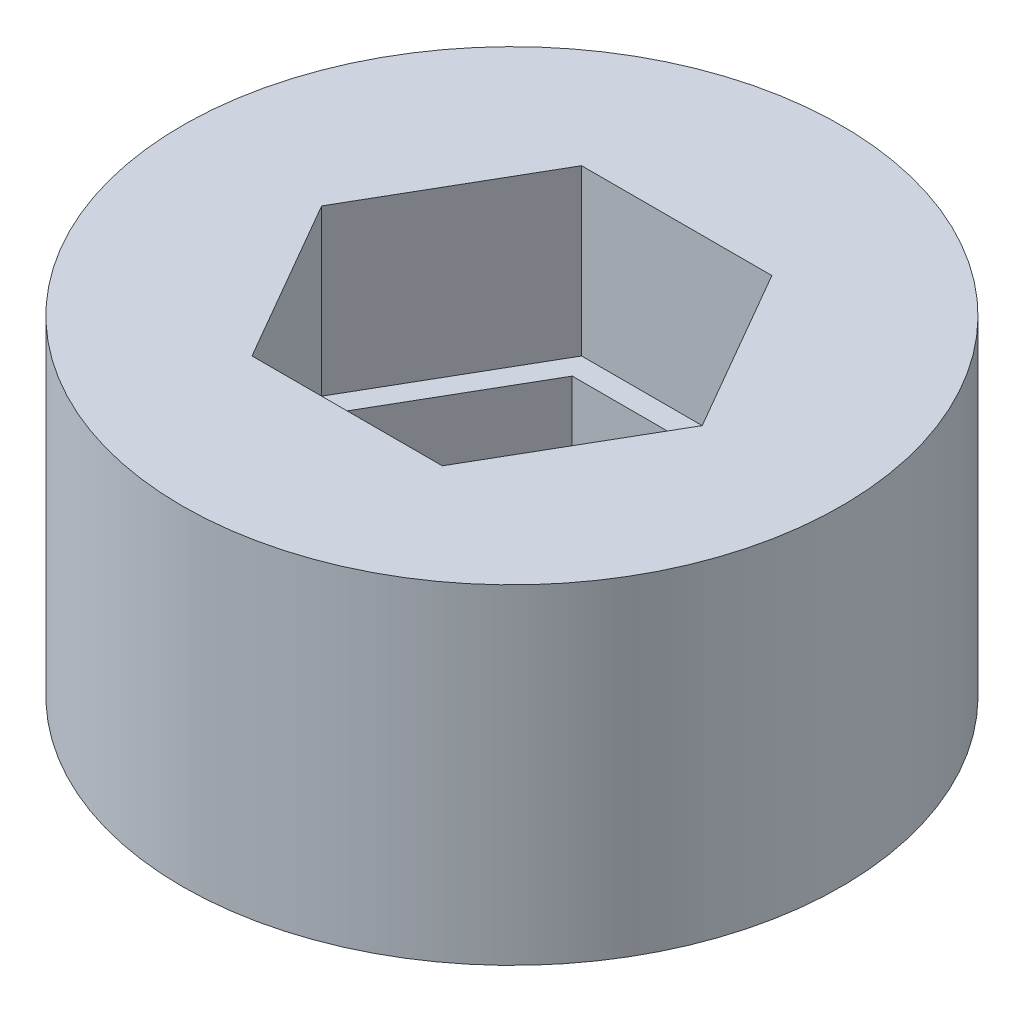
SolidWorks part; units mm, degrees
ref_plane "Front" through (0, 0, 0) normal (0, 0, 1) x (1, 0, 0)
ref_plane "Top" through (0, 0, 0) normal (0, 1, 0) x (1, 0, 0)
ref_plane "Right" through (0, 0, 0) normal (1, 0, 0) x (0, 0, -1)
sketch "Sketch1" plane through (0, 0, 0) normal (0, 1, 0) x (1, 0, 0)
  line L1 (1.5875, 2.7496) -> (-1.5875, 2.7496)
  line L2 (-1.5875, 2.7496) -> (-3.175, 0)
  line L3 (-3.175, 0) -> (-1.5875, -2.7496)
  line L4 (-1.5875, -2.7496) -> (1.5875, -2.7496)
  line L5 (1.5875, -2.7496) -> (3.175, 0)
  line L6 (3.175, 0) -> (1.5875, 2.7496)
  circle A0 centre (0, 0) radius 6.35
  circle A1 centre (0, 0) radius 3.175 construction
  dimension "D1" = 12.7
  dimension "D2" = 6.35
extrude "Boss-Extrude1" add sketch "Sketch1" along normal blind 3.175
sketch "Sketch2" plane through (0, 3.175, 0) normal (0, 1, 0) x (1, 0, 0)
  line L1 (1.8331, 3.175) -> (-1.8331, 3.175)
  line L2 (-1.8331, 3.175) -> (-3.6662, 0)
  line L3 (-3.6662, 0) -> (-1.8331, -3.175)
  line L4 (-1.8331, -3.175) -> (1.8331, -3.175)
  line L5 (1.8331, -3.175) -> (3.6662, 0)
  line L6 (3.6662, 0) -> (1.8331, 3.175)
  circle A0 centre (0, 0) radius 6.35 construction
  circle A1 centre (0, 0) radius 6.35
  circle A2 centre (0, 0) radius 3.175 construction
extrude "Boss-Extrude2" add sketch "Sketch2" along normal blind 3.175
